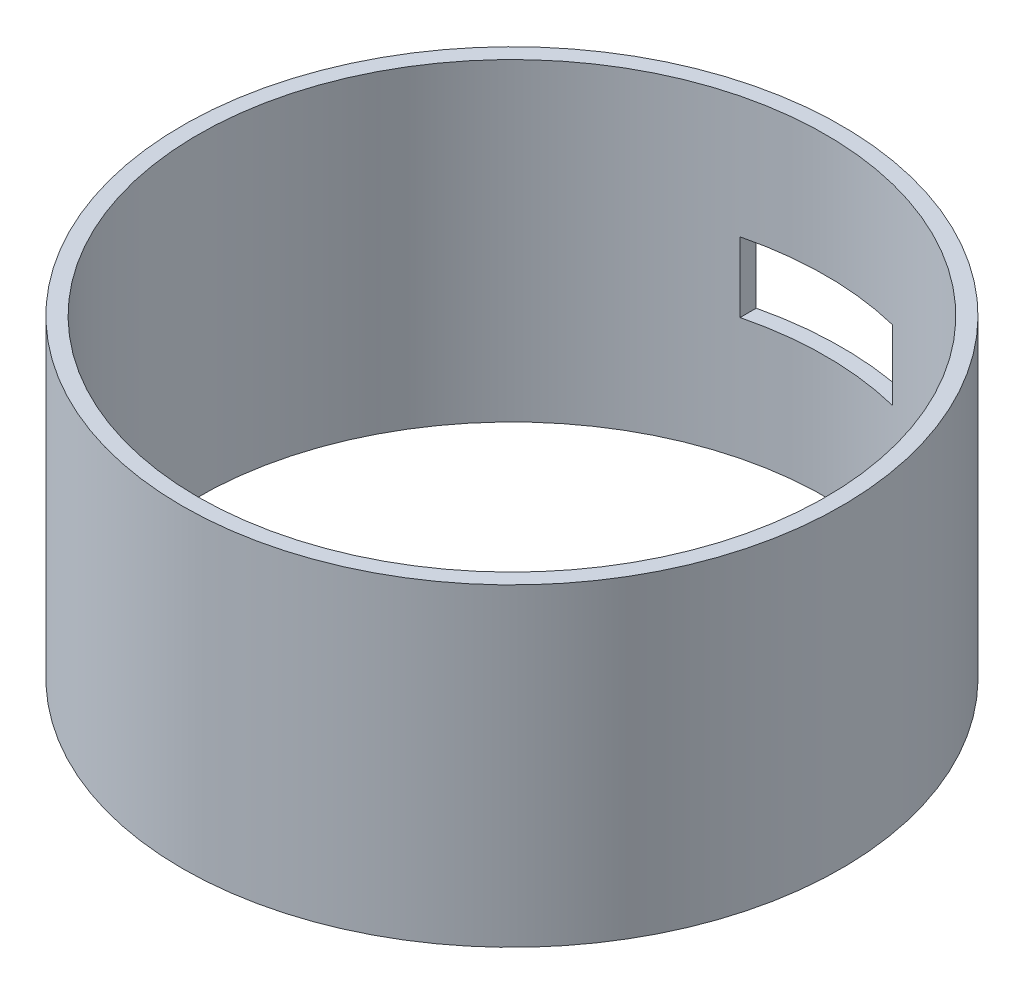
SolidWorks part; units mm, degrees
ref_plane "Front Plane" through (0, 0, 0) normal (0, 0, 1) x (1, 0, 0)
ref_plane "Top Plane" through (0, 0, 0) normal (0, 1, 0) x (1, 0, 0)
ref_plane "Right Plane" through (0, 0, 0) normal (1, 0, 0) x (0, 0, -1)
sketch "Sketch1" plane through (0, 0, 0) normal (0, 1, 0) x (1, 0, 0)
  circle A0 centre (0, 0) radius 105
  circle A1 centre (0, 0) radius 100
  dimension "D1" = 200
  dimension "D2" = 210
extrude "Boss-Extrude3" add sketch "Sketch1" along normal blind 100
sketch "Sketch2" plane through (0, 0, 0) normal (0, 0, 1) x (1, 0, 0)
  line L0 (-105, 50) -> (105, 50) construction
  line L1 (-105, 100) -> (-105, 0) construction
  line L2 (105, 0) -> (105, 100) construction
  line L3 (0, 0) -> (0, 100) construction
  line L4 (105, 100) -> (-105, 100) construction
  line L6 (24.3104, 61.128) -> (-24.3104, 61.128)
  line L7 (24.3104, 61.128) -> (24.3104, 38.872)
  line L8 (24.3104, 38.872) -> (-24.3104, 38.872)
  line L9 (-24.3104, 61.128) -> (-24.3104, 38.872)
  line L10 (24.3104, 61.128) -> (-24.3104, 38.872) construction
  line L11 (24.3104, 38.872) -> (-24.3104, 61.128) construction
  point P11 (0, 50)
  dimension "D1" = 48.6207
  dimension "D2" = 22.256
extrude "Cut-Extrude2" cut sketch "Sketch2" against normal blind 187
